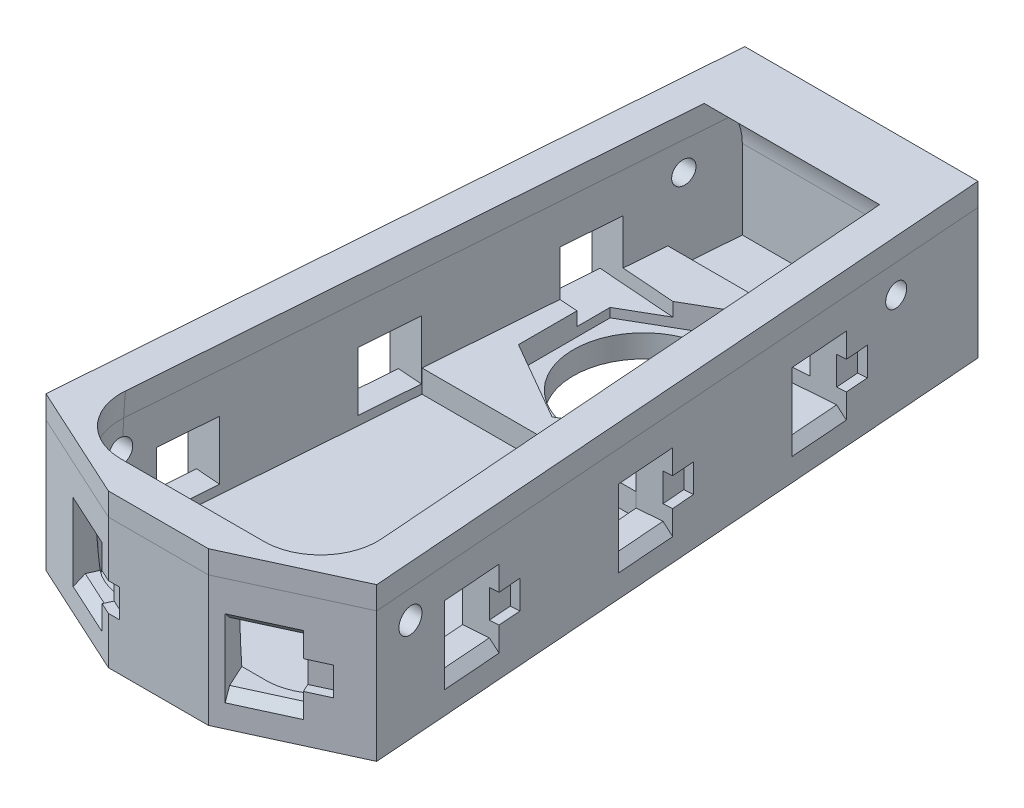
SolidWorks part; units mm, degrees
ref_plane "Front Plane" through (0, 0, 0) normal (0, 0, 1) x (1, 0, 0)
ref_plane "Top Plane" through (0, 0, 0) normal (0, 1, 0) x (1, 0, 0)
ref_plane "Right Plane" through (0, 0, 0) normal (1, 0, 0) x (0, 0, -1)
sketch "Sketch1" plane through (0, 0, 0) normal (0, 1, 0) x (1, 0, 0)
  line L0 (-14.7, 31) -> (-11.7, 28) construction
  line L1 (-11.7, 28) -> (11.7, 28) construction
  line L2 (-11.7, 28) -> (-11.7, -28) construction
  line L3 (-11.7, -28) -> (11.7, -28) construction
  line L4 (11.7, 28) -> (11.7, -28) construction
  line L5 (-14.7, 31) -> (14.7, 31)
  line L6 (-14.7, 31) -> (-14.7, -31)
  line L7 (-14.7, -31) -> (14.7, -31)
  line L8 (14.7, 31) -> (14.7, -31)
  line L9 (11.7, -28) -> (14.7, -31) construction
  line L10 (11.7, 28) -> (14.7, 31) construction
  line L11 (-11.7, -28) -> (-14.7, -31) construction
  line L12 (-11.7, -28) -> (-11.4, -27.7) construction
  line L13 (-11.4, 27.7) -> (11.4, 27.7) construction
  line L14 (-11.4, 27.7) -> (-11.4, -27.7) construction
  line L15 (-11.4, -27.7) -> (11.4, -27.7) construction
  line L16 (11.4, 27.7) -> (11.4, -27.7) construction
  line L17 (11.4, -27.7) -> (11.7, -28) construction
  line L18 (11.4, 27.7) -> (11.7, 28) construction
  line L19 (-11.7, 28) -> (-11.4, 27.7) construction
  line L20 (-7.9914, 28) -> (-7.9914, 31) construction
  line L21 (-11.7, 2.2384) -> (-14.7, 2.2384) construction
  line L22 (-7.9914, 28) -> (-7.9914, 27.7) construction
  line L23 (-11.7, 2.2384) -> (-11.4, 2.2384) construction
  line L26 (-11.4, 27.7) -> (11.4, -27.7) construction
  point P16 (0, 0)
  dimension "D1" = 3
  dimension "D2" = 0.3
  dimension "D3" = 29.4
  dimension "D4" = 62
extrude "Boss-Extrude1" add sketch "Sketch1" against normal blind 11.5
sketch "Sketch3" plane through (0, 0, 0) normal (1, 0, 0) x (0, 0, -1)
  line L3 (28, -4.5) -> (28, -55.6727)
  line L4 (28, 0) -> (28, -4.5) construction
  line L5 (28, 0) -> (23.2, 0) construction
  line L6 (28, 0) -> (31, 0) construction
  line L8 (-27.6988, 0) -> (-28, 0)
  line L9 (24.8703, 0) -> (23.2, 0)
  line L11 (23.2, 0) -> (-27.6988, 0)
  arc A0 (-28, 0) -> (28, -55.6727) centre (23.2, -4.5) ccw
  circle A1 centre (23.2, -4.5) radius 1 construction
  circle A2 centre (23.2, -4.5) radius 4.8 construction
  circle A3 centre (23.2, -4.5) radius 4.5 construction
  circle A5 centre (23.2, -4.5) radius 51.0974 construction
  arc A6 (28, -4.5) -> (24.8703, 0) centre (23.2, -4.5) ccw
  dimension "D1" = 2
  dimension "D3" = 0.3
  dimension "D4" = 3
  dimension "D5" = 0.3
  dimension "D6" = 9
extrude "Cut-Extrude2" cut sketch "Sketch3" against normal up to vertex (11.7 mm away) and the other way up to vertex (11.7 mm away) up to point (-11.7, 0, -28) other way up to point (11.7, 0, -28)
sketch "Sketch6" plane through (0, 0, 0) normal (0, 1, 0) x (1, 0, 0)
  line L0 (-11.7, 28) -> (-11.7, -28)
  line L1 (-11.7, -28) -> (-7.5, 28)
  line L3 (-7.5, 28) -> (-11.7, 28)
  line L4 (11.7, 28) -> (7.5, 28)
  line L5 (7.5, 28) -> (11.7, -28)
  line L6 (11.7, -28) -> (11.7, 28)
  dimension "D1" = 15
extrude "Boss-Extrude3" add sketch "Sketch6" against normal up to vertex (11.5 mm away) up to point (-11.7, -11.5, -28)
sketch "Sketch4" plane through (0, 0, 0) normal (1, 0, 0) x (0, 0, -1)
  circle A0 centre (23.2, -4.5) radius 1
  circle A1 centre (23.2, -4.5) radius 1 construction
  dimension "D1" = 2
extrude "Cut-Extrude3" cut sketch "Sketch4" against normal through all both and the other way through all
fillet "Fillet1" radius 5 2 edges at (-11.7, -4.5, 28.1974) (11.7, -4.5, 28.1974)
sketch "Sketch7" plane through (0, -11.5, 0) normal (0, -1, 0) x (-1, 0, 0)
  line L0 (0, 0) -> (0, 14.5109) construction
  line L1 (14.7, 31) -> (-14.7, 31)
  line L2 (14.7, 31) -> (14.7, -31)
  line L3 (14.7, -31) -> (-14.7, -31)
  line L4 (-14.7, 31) -> (-14.7, -31)
  line L8 (14.7, 23.2) -> (-14.7, 23.2) construction
  line L9 (-14.7, 24.2) -> (-14.7, 22.2) construction
  line L10 (14.7, 20.2) -> (-14.7, 20.2) construction
  circle A2 centre (0, 11.8) radius 6.2
  dimension "D1" = 12.4
  dimension "D2" = 3
  dimension "D3" = 19.2
extrude "Boss-Extrude4" add sketch "Sketch7" along normal blind 2
sketch "Sketch8" plane through (0, -11.5, 0) normal (0, 1, 0) x (1, 0, 0)
  line L1 (-9.4712, 1.7171) -> (9.4712, 1.7171)
  line L4 (-11.2719, -22.2923) -> (-7.5, 28) construction
  line L6 (7.5, 28) -> (11.2719, -22.2923) construction
  line L11 (9.4712, 1.7171) -> (7.9588, 21.8829)
  line L12 (7, 7.7585) -> (7, 15.8415)
  line L13 (7, 15.8415) -> (0, 19.8829)
  line L14 (0, 19.8829) -> (-7, 15.8415)
  line L15 (-7, 15.8415) -> (-7, 7.7585)
  line L16 (-7, 7.7585) -> (0, 3.7171)
  line L17 (0, 3.7171) -> (7, 7.7585)
  line L18 (7.9588, 21.8829) -> (-7.9588, 21.8829)
  line L19 (-7.9588, 21.8829) -> (-9.4712, 1.7171)
  circle A0 centre (0, 11.8) radius 7 construction
  dimension "D1" = 14
  dimension "D2" = 2
  dimension "D3" = 2
extrude "Boss-Extrude5" add sketch "Sketch8" along normal blind 2
sketch "Sketch9" plane through (-14.7, 0, 0) normal (-1, 0, 0) x (0, 0, 1)
  line L0 (-23.2, -4.5) -> (23.109, -4.4527) construction
  line L2 (22.9995, -7.6832) -> (-23.2, -4.5) construction
  circle A0 centre (23.109, -4.4527) radius 1.1
  arc A1 (21.709, -4.4541) -> (24.509, -4.4513) centre (23.109, -4.4527) cw construction
  arc A2 (21.709, -4.4541) -> (21.6028, -7.5869) centre (-23.2, -4.5) cw construction
  arc A3 (24.509, -4.4513) -> (24.3962, -7.7794) centre (-23.2, -4.5) cw construction
  arc A4 (24.3962, -7.7794) -> (21.6028, -7.5869) centre (22.9995, -7.6832) cw construction
  dimension "D1" = 2.2
  dimension "D3" = 4
  dimension "D2" = 0.3
extrude "Cut-Extrude4" cut sketch "Sketch9" against normal through all
sketch "Sketch15" plane through (0, 0, 0) normal (0, 1, 0) x (1, 0, 0)
  line L0 (-10.2834, 31) -> (-14.7, -27.8877)
  line L1 (14.7, 31) -> (-14.7, 31) construction
  line L2 (10.2834, 31) -> (14.7, -27.8877)
  line L3 (14.7, -31) -> (14.7, 31) construction
  line L4 (14.7, -27.8877) -> (14.7, 31)
  line L5 (14.7, 31) -> (10.2834, 31)
  line L6 (-10.2834, 31) -> (-14.7, 31)
  line L7 (-14.7, 31) -> (-14.7, -27.8877)
  line L9 (-11.2954, -22.6047) -> (-7.7347, 24.8703) construction
  line L10 (7.7347, 24.8703) -> (11.2954, -22.6047) construction
  dimension "D1" = 3
extrude "Cut-Extrude7" cut sketch "Sketch15" against normal through all
sketch "Sketch12" plane through (0, 0, 0) normal (0, 1, 0) x (1, 0, 0)
  line L0 (-14.7, -26.2735) -> (-4.4092, -31)
  line L1 (-14.7, -27.8877) -> (-14.7, -31) construction
  line L2 (-4.4092, -31) -> (-14.7, -31)
  line L3 (-14.7, -31) -> (-14.7, -26.2735)
  line L5 (14.7, -31) -> (14.7, -26.2735)
  line L6 (14.7, -31) -> (14.7, -27.8877) construction
  line L8 (14.7, -31) -> (4.4092, -31)
  line L9 (-14.7, -31) -> (14.7, -31) construction
  line L10 (4.4092, -31) -> (14.7, -26.2735)
  line M13 (-14.7, -27.8877) -> (-14.7, -31)
  line M14 (-14.7, -31) -> (14.7, -31)
  line M15 (14.7, -31) -> (14.7, -27.8877)
extrude "Cut-Extrude5" cut sketch "Sketch12" against normal through all contours L0 M13 M14 | L10 M14 M15
sketch "Sketch14" plane through (0, 0, 31) normal (0, 0, 1) x (1, 0, 0)
  line L0 (-8.5, -7.1757) -> (8.5, -7.1757)
  line L1 (-4.4092, 0) -> (4.4092, 0) construction
  point P4 (0, 0)
  point P5 (0, -7.1757)
  dimension "D1" = 17
sketch "Sketch13" plane through (-12.5259, 0, 27.272) normal (-0.4174, 0, 0.9087) x (0.9087, 0, 0.4174)
  line L0 (-2.3924, 0) -> (8.9319, 0) construction
  line L1 (2.6145, -5.5) -> (7.8145, -5.5)
  line L2 (2.6145, -5.5) -> (2.6145, -10.7)
  line L3 (2.6145, -10.7) -> (7.8145, -10.7)
  line L4 (7.8145, -5.5) -> (7.8145, -10.7)
  line L5 (5.2145, -5.5) -> (5.2145, -10.7) construction
  dimension "D1" = 5.5
  dimension "D2" = 5.2
extrude "Cut-Extrude6" cut sketch "Sketch13" against normal blind 10
sketch "Sketch16" plane through (-12.5379, 0, -0.9403) normal (-0.9972, 0, -0.0748) x (-0.0748, 0, 0.9972)
  line L0 (-12.3559, -5.5) -> (-0.9559, -5.5) construction
  line L1 (20.8441, -5.5) -> (15.6441, -5.5)
  line L2 (20.8441, -5.5) -> (20.8441, -10.7)
  line L3 (20.8441, -10.7) -> (15.6441, -10.7)
  line L4 (15.6441, -5.5) -> (15.6441, -10.7)
  line L5 (4.2441, -5.5) -> (-0.9559, -5.5)
  line L6 (4.2441, -5.5) -> (4.2441, -10.7)
  line L7 (4.2441, -10.7) -> (-0.9559, -10.7)
  line L8 (-0.9559, -5.5) -> (-0.9559, -10.7)
  line L9 (-12.3559, -5.5) -> (-17.5559, -5.5)
  line L10 (-12.3559, -5.5) -> (-12.3559, -10.7)
  line L11 (-12.3559, -10.7) -> (-17.5559, -10.7)
  line L12 (-17.5559, -5.5) -> (-17.5559, -10.7)
  line L13 (4.2441, -5.5) -> (15.6441, -5.5) construction
  line L14 (20.8441, -5.5) -> (34.388, -5.5) construction
  line L15 (20.8441, -10.7) -> (32.1529, -10.7) construction
  line L16 (15.6441, -10.7) -> (4.2441, -10.7) construction
  line L17 (-0.9559, -10.7) -> (-12.3559, -10.7) construction
  line L19 (27.3441, -13.5) -> (27.3441, 0) construction
  dimension "D1" = 16.6
  dimension "D2" = 6.5
extrude "Cut-Extrude8" cut sketch "Sketch16" against normal blind 10
mirror "Mirror1" about plane through (0, 0, 0) normal (1, 0, 0) of "Cut-Extrude8", "Cut-Extrude6"
chamfer "Chamfer1" distance 0.8 angle 45 16 edges at (7.7874, -5.5, 29.4484) (7.7874, -10.7, 29.4484) (-7.7874, -5.5, 29.4484) (-13.9024, -5.5, 17.2527) (-12.6609, -5.5, 0.6992) (-11.4194, -5.5, -15.8543) (-7.7874, -10.7, 29.4484) (-13.9024, -10.7, 17.2527) (-12.6609, -10.7, 0.6992) (-11.4194, -10.7, -15.8543) (11.4194, -5.5, -15.8543) (11.4194, -10.7, -15.8543) (12.6609, -5.5, 0.6992) (12.6609, -10.7, 0.6992) (13.9024, -5.5, 17.2527) (13.9024, -10.7, 17.2527)
sketch "Sketch17" plane through (-12.5379, 0, -0.9403) normal (-0.9972, 0, -0.0748) x (-0.0748, 0, 0.9972)
  line L0 (-12.3559, -11.5) -> (-12.3559, -4.7) construction
  line L1 (-12.3559, -6.85) -> (-10.3559, -6.85)
  line L2 (-12.3559, -6.85) -> (-12.3559, -9.35)
  line L3 (-12.3559, -9.35) -> (-10.3559, -9.35)
  line L4 (-10.3559, -6.85) -> (-10.3559, -9.35)
  line L5 (4.2441, -6.85) -> (6.2441, -6.85)
  line L6 (4.2441, -6.85) -> (4.2441, -9.35)
  line L7 (4.2441, -9.35) -> (6.2441, -9.35)
  line L8 (6.2441, -6.85) -> (6.2441, -9.35)
  line L9 (20.8441, -6.85) -> (22.8441, -6.85)
  line L10 (20.8441, -6.85) -> (20.8441, -9.35)
  line L11 (20.8441, -9.35) -> (22.8441, -9.35)
  line L12 (22.8441, -6.85) -> (22.8441, -9.35)
  line L13 (4.2441, -11.5) -> (4.2441, -4.7) construction
  line L14 (20.8441, -11.5) -> (20.8441, -4.7) construction
  point P15 (-12.3559, -8.1)
  dimension "D1" = 2.5
  dimension "D2" = 2
extrude "Cut-Extrude9" cut sketch "Sketch17" against normal blind 0.8
sketch "Sketch18" plane through (-12.5259, 0, 27.272) normal (-0.4174, 0, 0.9087) x (0.9087, 0, 0.4174)
  line L0 (7.8145, -11.5) -> (7.8145, -4.7) construction
  line L1 (7.8145, -6.85) -> (9.8145, -6.85)
  line L2 (7.8145, -6.85) -> (7.8145, -9.35)
  line L3 (7.8145, -9.35) -> (9.8145, -9.35)
  line L4 (9.8145, -6.85) -> (9.8145, -9.35)
  line L6 (-4.5272, -9.35) -> (-3.8307, -9.35) construction
  line L7 (-3.8307, -6.85) -> (-4.5272, -6.85) construction
  dimension "D1" = 2
extrude "Cut-Extrude10" cut sketch "Sketch18" against normal blind 0.8
sketch "Sketch19" plane through (12.5259, 0, 27.272) normal (0.4174, 0, 0.9087) x (0.9087, 0, -0.4174)
  line L0 (-2.6145, -4.7) -> (-2.6145, -11.5) construction
  line L1 (-2.6145, -6.85) -> (-0.6145, -6.85)
  line L2 (-2.6145, -6.85) -> (-2.6145, -9.35)
  line L3 (-2.6145, -9.35) -> (-0.6145, -9.35)
  line L4 (-0.6145, -6.85) -> (-0.6145, -9.35)
  line L5 (-16.9455, -9.35) -> (-16.0629, -9.35) construction
  line L6 (-16.0629, -6.85) -> (-16.9455, -6.85) construction
  dimension "D1" = 2
extrude "Cut-Extrude11" cut sketch "Sketch19" against normal blind 0.8
sketch "Sketch20" plane through (12.5379, 0, -0.9403) normal (0.9972, 0, -0.0748) x (-0.0748, 0, -0.9972)
  line L0 (-15.6441, -4.7) -> (-15.6441, -11.5) construction
  line L1 (-15.6441, -6.85) -> (-13.6441, -6.85)
  line L2 (-15.6441, -6.85) -> (-15.6441, -9.35)
  line L3 (-15.6441, -9.35) -> (-13.6441, -9.35)
  line L4 (-13.6441, -6.85) -> (-13.6441, -9.35)
  line L5 (0.9559, -4.7) -> (0.9559, -11.5) construction
  line L6 (0.9559, -6.85) -> (2.9559, -6.85)
  line L7 (0.9559, -6.85) -> (0.9559, -9.35)
  line L8 (0.9559, -9.35) -> (2.9559, -9.35)
  line L9 (2.9559, -6.85) -> (2.9559, -9.35)
  line L10 (17.5559, -4.7) -> (17.5559, -11.5) construction
  line L11 (17.5559, -6.85) -> (19.5559, -6.85)
  line L12 (17.5559, -6.85) -> (17.5559, -9.35)
  line L13 (17.5559, -9.35) -> (19.5559, -9.35)
  line L14 (19.5559, -6.85) -> (19.5559, -9.35)
  line L15 (-28.3464, -6.85) -> (-29.0429, -6.85) construction
  line L16 (-29.0429, -9.35) -> (-28.3464, -9.35) construction
  dimension "D1" = 2
extrude "Cut-Extrude12" cut sketch "Sketch20" against normal blind 0.8
ref_plane "Plane1" through (0, -2, 0) normal (0, 1, 0) x (1, 0, 0)
split "Split1" trim tools "Plane1" bodies to split 118 resulting bodies 120 121
sketch "Sketch22" plane through (0, 0, 0) normal (0, 1, 0) x (1, 0, 0)
  line L0 (-7.7347, 24.8703) -> (7.7347, 24.8703) construction
  line L1 (7.7347, 24.8703) -> (11.2954, -22.6047) construction
  line L2 (-6.3124, -28) -> (6.3124, -28) construction
  line L3 (-11.2954, -22.6047) -> (-7.7347, 24.8703) construction
  line L4 (-7.7347, 24.8703) -> (7.7347, 24.8703)
  line L5 (7.7347, 24.8703) -> (11.2954, -22.6047)
  line L6 (-10.2834, 31) -> (-14.583, -26.3272)
  line L7 (-14.583, -26.3272) -> (-4.4092, -31)
  line L8 (-4.4092, -31) -> (4.4092, -31)
  line L9 (4.4092, -31) -> (14.583, -26.3272)
  line L10 (14.583, -26.3272) -> (10.2834, 31)
  line L11 (10.2834, 31) -> (-10.2834, 31)
  line L12 (-10.2834, 31) -> (-14.583, -26.3272)
  line L13 (-14.583, -26.3272) -> (-4.4092, -31)
  line L14 (-4.4092, -31) -> (4.4092, -31)
  line L15 (4.4092, -31) -> (14.583, -26.3272)
  line L16 (14.583, -26.3272) -> (10.2834, 31)
  line L17 (10.2834, 31) -> (-10.2834, 31)
  line L18 (-6.3124, -28) -> (6.3124, -28)
  line L19 (-11.2954, -22.6047) -> (-7.7347, 24.8703)
  spline S0 degree 3 poles (-1968.3707, 257.7108) (-275.3119, 66.9232) (15.3505, 7.8087) (11.2235, -23.9709) (11.1435, -24.3105) (10.9184, -24.9592) (10.774, -25.2689) (10.5097, -25.7115) (10.4129, -25.8561) (10.2067, -26.1321) (10.0972, -26.2639) (9.7498, -26.641) (9.4924, -26.869) (8.9293, -27.2715) (8.6317, -27.4404) (8.0054, -27.7159) (7.673, -27.8229) (-26.1883, -34.9386) (-110.8332, 304.4922) (-385.5988, 1932.5075) knots -11.464737 -11.464737 -11.464737 -11.464737 0.125 0.125 0.25 0.25 0.375 0.375 0.4375 0.4375 0.5 0.5 0.625 0.625 0.75 0.75 0.875 0.875 13.337611 13.337611 13.337611 13.337611 only from (11.2954, -22.6047) to (6.3124, -28) construction
  spline S1 degree 3 poles (420.8125, 1925.2378) (103.2625, 248.1145) (23.3533, -34.3272) (-7.6691, -27.8239) (-8.0016, -27.7174) (-8.6301, -27.4414) (-8.9272, -27.2726) (-9.3473, -26.9729) (-9.4836, -26.8646) (-9.7416, -26.6368) (-9.864, -26.517) (-10.2115, -26.14) (-10.4184, -25.8638) (-10.7732, -25.2709) (-10.9176, -24.9608) (-11.1425, -24.3141) (-11.2229, -23.9741) (-15.6788, 10.2317) (322.7828, 69.7487) (1972.3372, 227.3531) knots -11.335333 -11.335333 -11.335333 -11.335333 0.125 0.125 0.25 0.25 0.375 0.375 0.4375 0.4375 0.5 0.5 0.625 0.625 0.75 0.75 0.875 0.875 13.310858 13.310858 13.310858 13.310858 only from (-6.3124, -28) to (-11.2954, -22.6047) construction
  spline S2 degree 3 poles (11.2954, -22.6047) (11.3213, -22.9504) (11.3115, -23.2927) (11.2235, -23.9709) (11.1435, -24.3105) (10.9184, -24.9592) (10.774, -25.2689) (10.5097, -25.7115) (10.4129, -25.8561) (10.2067, -26.1321) (10.0972, -26.2639) (9.7498, -26.641) (9.4924, -26.869) (8.9293, -27.2715) (8.6317, -27.4404) (8.0054, -27.7159) (7.673, -27.8229) (7.0005, -27.9642) (6.6591, -28) (6.3124, -28) knots 0 0 0 0 0.125 0.125 0.25 0.25 0.375 0.375 0.4375 0.4375 0.5 0.5 0.625 0.625 0.75 0.75 0.875 0.875 1 1 1 1
  spline S3 degree 3 poles (-6.3124, -28) (-6.6591, -28) (-6.9996, -27.9642) (-7.6691, -27.8239) (-8.0016, -27.7174) (-8.6301, -27.4414) (-8.9272, -27.2726) (-9.3473, -26.9729) (-9.4836, -26.8646) (-9.7416, -26.6368) (-9.864, -26.517) (-10.2115, -26.14) (-10.4184, -25.8638) (-10.7732, -25.2709) (-10.9176, -24.9608) (-11.1425, -24.3141) (-11.2229, -23.9741) (-11.3116, -23.2933) (-11.3213, -22.9503) (-11.2954, -22.6047) knots 0 0 0 0 0.125 0.125 0.25 0.25 0.375 0.375 0.4375 0.4375 0.5 0.5 0.625 0.625 0.75 0.75 0.875 0.875 1 1 1 1
  point P6 (0, -31)
  dimension "D1" = 0
